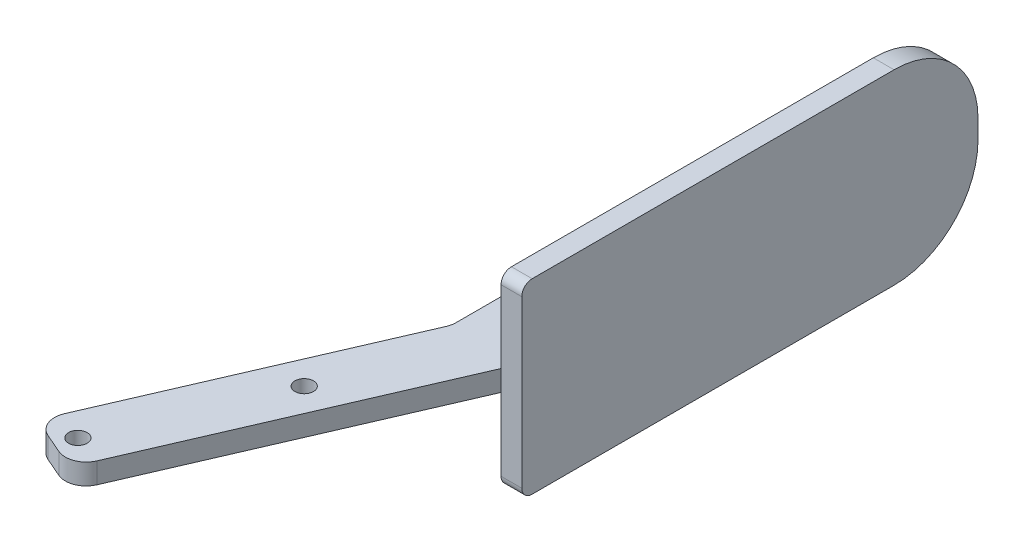
SolidWorks part; units mm, degrees
ref_plane "Front Plane" through (0, 0, 0) normal (0, 0, 1) x (1, 0, 0)
ref_plane "Top Plane" through (0, 0, 0) normal (0, 1, 0) x (1, 0, 0)
ref_plane "Right Plane" through (0, 0, 0) normal (1, 0, 0) x (0, 0, -1)
sketch "Sketch1" plane through (0, 0, 0) normal (1, 0, 0) x (0, 0, -1)
  line L0 (0, 0) -> (69.85, 0) construction
  line L1 (0, 14.2875) -> (69.85, 14.2875)
  line L2 (0, 14.2875) -> (0, -14.2875)
  line L3 (0, -14.2875) -> (69.85, -14.2875)
  line L4 (69.85, 14.2875) -> (69.85, -14.2875)
  dimension "D1" = 28.575
  dimension "D2" = 69.85
extrude "Boss-Extrude1" add sketch "Sketch1" along normal blind 3.175
fillet "Fillet1" radius 12.8524 2 edges at (1.5875, -14.2875, -69.85) (1.5875, 14.2875, -69.85)
sketch "Sketch4" plane through (0, 0, 0) normal (0, 1, 0) x (1, 0, 0)
  line L0 (0, 0) -> (-19.9502, -46.101)
  line L1 (-19.9502, -46.101) -> (-28.6918, -42.3181)
  line L2 (-28.6918, -42.3181) -> (-9.525, 1.9726)
  line L3 (-9.525, 1.9726) -> (-9.525, 55.499)
  line L4 (-9.525, 55.499) -> (0, 55.499)
  line L5 (0, 55.499) -> (0, 0)
  line L6 (0, 69.85) -> (3.175, 69.85) construction
  dimension "D1" = 9.525
  dimension "D2" = 14.351
  dimension "D3" = 101.6
  dimension "D4" = 48.26
extrude "Boss-Extrude2" add sketch "Sketch4" along normal mid plane 3.175
fillet "Fillet2" radius 1.5875 2 edges at (1.5875, -14.2875, 0) (1.5875, 14.2875, 0)
fillet "Fillet3" radius 3.175 4 edges at (-9.525, 0, -55.499) (-9.525, 0, -1.9726) (-19.9502, 0, 46.101) (-28.6918, 0, 42.3181)
hole_wizard "Hole1" positions "Sketch6" profile "Sketch5" legacy end condition through all
sketch "Sketch6" plane through (0, 1.5875, 0) normal (0, 1, 0) x (-1, 0, 0)
  line L0 (24.321, 44.2095) -> (23.1911, 41.5987) construction
  line L1 (25.7779, 43.5791) -> (22.864, 44.84) construction
  line L4 (18.6892, 43.1871) -> (0, 0) construction
  point P0 (23.1911, 41.5987)
  dimension "D1" = 2.8448
sketch "Sketch5" plane through (-23.1911, 1.5875, 41.5987) normal (1, 0, 0) x (0, 0, 1)
  line L0 (0, 0) -> (0, 15.875)
  line L1 (0, 15.875) -> (1.4224, 15.875)
  line L2 (1.4224, 15.875) -> (1.4224, 0)
  line L3 (1.4224, 0) -> (0, 0)
  line L4 (0, 110) -> (0, -10) construction
  dimension "Diameter" = 2.8448
  dimension "Depth" = 15.875
pattern_linear "LPattern1" count 2 spacing 26.3525 along (0.3972, 0, -0.9178) of "Hole1"
ref_point "Point1"
ref_point "Point2"
